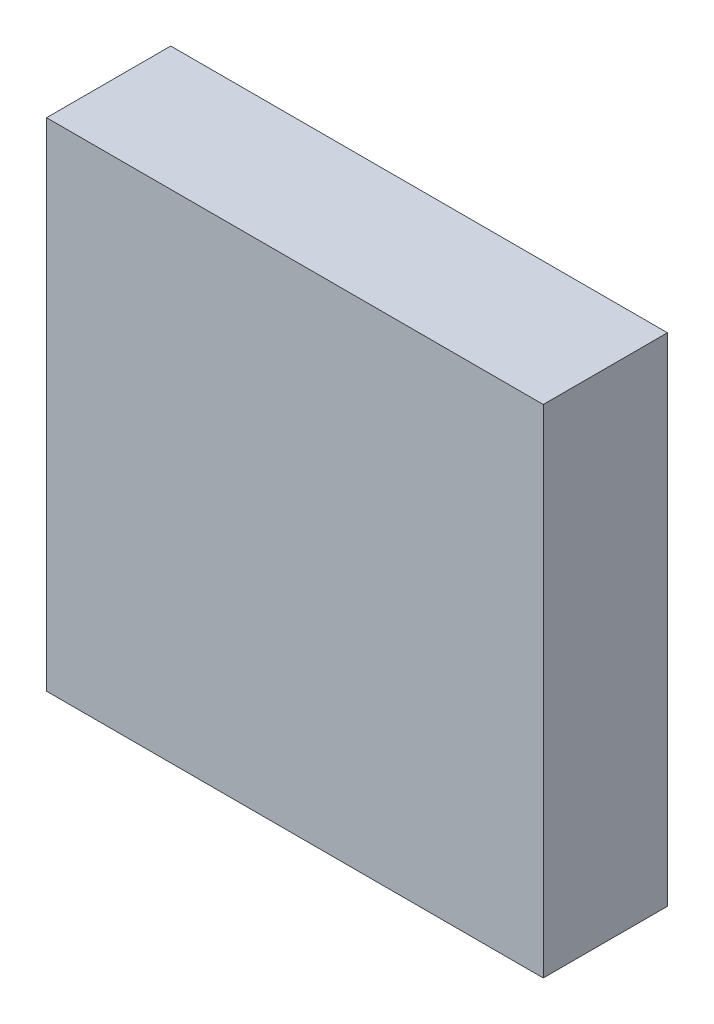
SolidWorks part; units mm, degrees
ref_plane "Front Plane" through (0, 0, 0) normal (0, 0, 1) x (1, 0, 0)
ref_plane "Top Plane" through (0, 0, 0) normal (0, 1, 0) x (1, 0, 0)
ref_plane "Right Plane" through (0, 0, 0) normal (1, 0, 0) x (0, 0, -1)
sketch "Sketch1" plane through (0, 0, 0) normal (0, 0, 1) x (1, 0, 0)
  line L1 (-152.4, 152.4) -> (152.4, 152.4)
  line L2 (-152.4, 152.4) -> (-152.4, -152.4)
  line L3 (-152.4, -152.4) -> (152.4, -152.4)
  line L4 (152.4, 152.4) -> (152.4, -152.4)
  line L5 (-152.4, 152.4) -> (152.4, -152.4) construction
  line L6 (-152.4, -152.4) -> (152.4, 152.4) construction
  point P0 (0, 0)
  dimension "D1" = 304.8
  dimension "D2" = 304.8
extrude "Boss-Extrude1" add sketch "Sketch1" along normal blind 76.2
sketch "Sketch2" plane through (0, 0, 0) normal (0, 0, -1) x (-1, 0, 0)
  circle A0 centre (0, 0) radius 3.175
  dimension "D1" = 6.35
extrude "Cut-Extrude1" cut sketch "Sketch2" against normal blind 2.54
